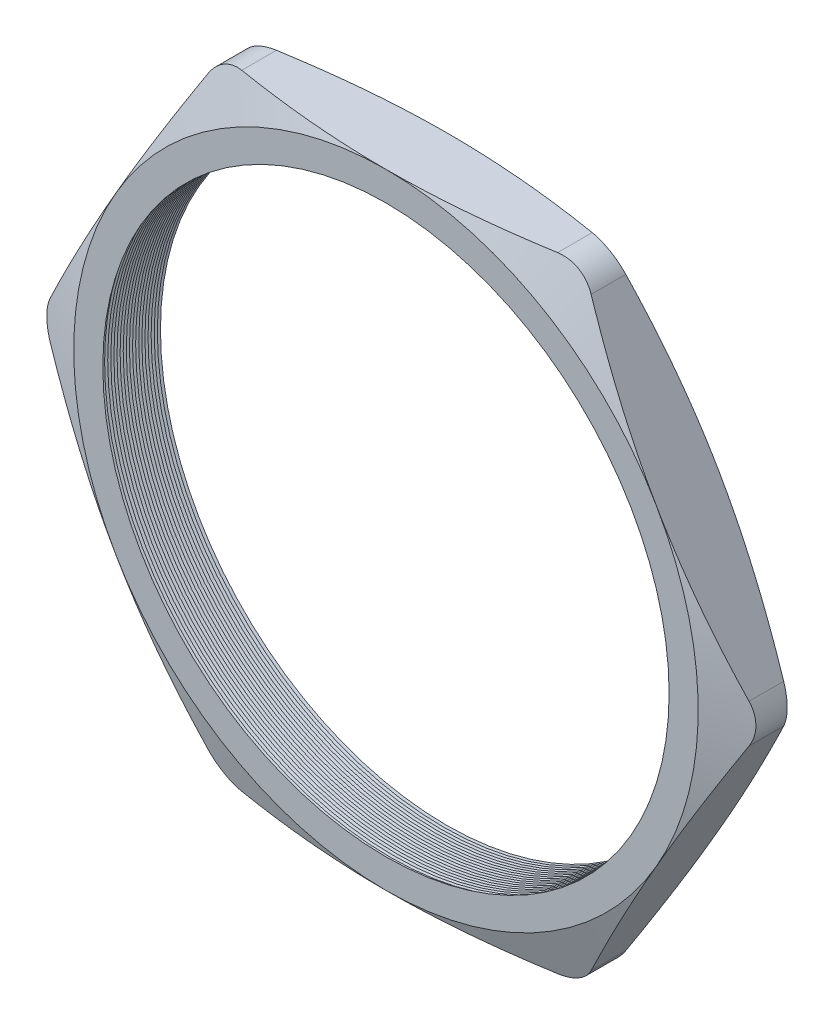
SolidWorks part; units mm, degrees
ref_plane "Front Plane" through (0, 0, 0) normal (0, 0, 1) x (1, 0, 0)
ref_plane "Top Plane" through (0, 0, 0) normal (0, 1, 0) x (1, 0, 0)
ref_plane "Right Plane" through (0, 0, 0) normal (1, 0, 0) x (0, 0, -1)
sketch "Sketch1" plane through (0, 0, 0) normal (0, 0, 1) x (1, 0, 0)
  line L1 (-23.6102, 0) -> (-11.8051, -20.447)
  line L2 (-11.8051, -20.447) -> (11.8051, -20.447)
  line L3 (11.8051, -20.447) -> (23.6102, 0)
  line L4 (23.6102, 0) -> (11.8051, 20.447)
  line L5 (11.8051, 20.447) -> (-11.8051, 20.447)
  line L6 (-11.8051, 20.447) -> (-23.6102, 0)
  circle A0 centre (0, 0) radius 20.447 construction
  circle A1 centre (0, 0) radius 18.542
  dimension "TS" = 37.084
  dimension "H" = 40.894
extrude "Extrude1" add sketch "Sketch1" along normal blind 4.064
fillet "Fillet1" radius 2.54 6 edges at (-11.8051, 20.447, 2.032) (-23.6102, 0, 2.032) (-11.8051, -20.447, 2.032) (11.8051, -20.447, 2.032) (23.6102, 0, 2.032) (11.8051, 20.447, 2.032)
sketch "Sketch2" plane through (0, 0, 4.064) normal (0, 0, 1) x (1, 0, 0)
  line L0 (10.3386, 20.447) -> (-10.3386, 20.447) construction
  circle A0 centre (0, 0) radius 20.447
extrude "Cut-Extrude1" cut sketch "Sketch2" against normal through all draft 70 flip side to cut
sketch "Sketch3" plane through (0, 0, 0) normal (0, 0, -1) x (-1, 0, 0)
  circle A0 centre (0, 0) radius 20.447
extrude "Cut-Extrude2" cut sketch "Sketch3" against normal through all draft 70 flip side to cut
sketch "Sketch4" plane through (0, 0, 0) normal (0, 1, 0) x (1, 0, 0)
  line L0 (-18.542, -4.064) -> (-18.542, -3.6241)
  line L2 (-18.542, -3.6241) -> (-18.923, -3.844)
  line L3 (-18.923, -3.844) -> (-18.542, -4.064)
  line L5 (-18.542, 0) -> (-18.542, -4.064) construction
  line L6 (-18.542, -4.064) -> (18.542, -4.064) construction
  dimension "D1" = 60
  dimension "D2" = 60
  dimension "D3" = 0.381
revolve "Cut-Revolve1" cut sketch "Sketch4" angle 360 about axis through (0, 0, 4.064) along (0, 0, -1)
pattern_linear "LPattern1" count 20 spacing 0.2032 along (0, 0, -1) of "Cut-Revolve1"
